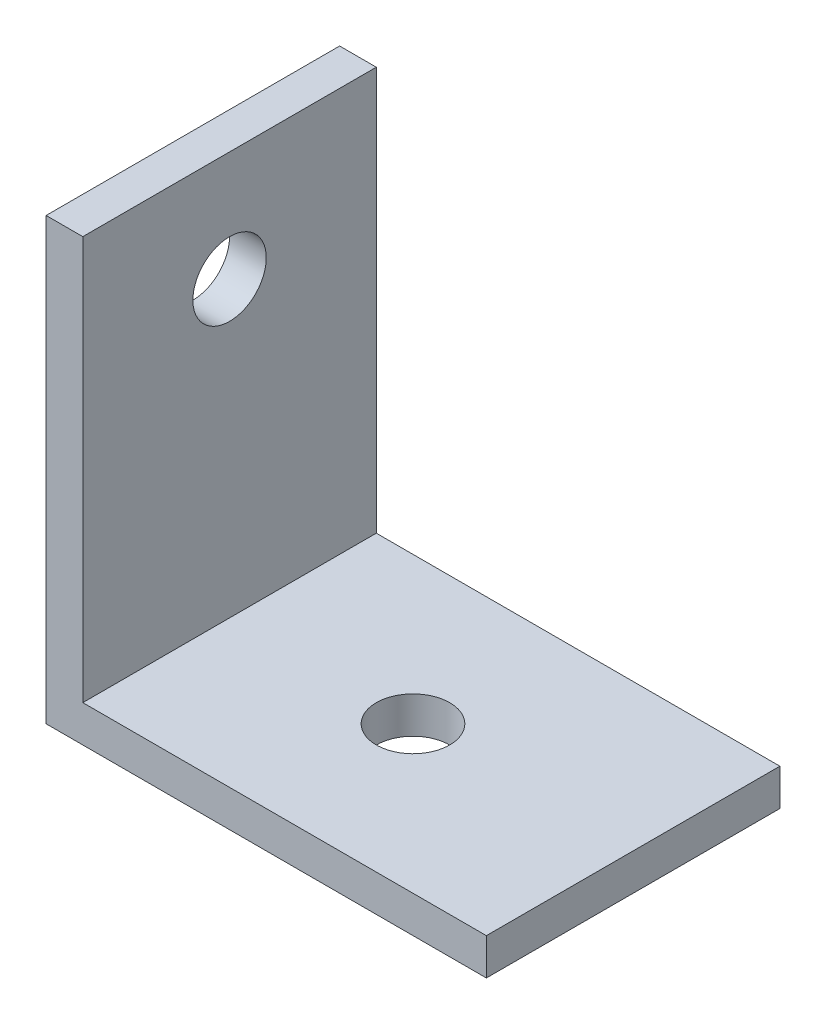
SolidWorks part; units mm, degrees
ref_plane "Front Plane" through (0, 0, 0) normal (0, 0, 1) x (1, 0, 0)
ref_plane "Top Plane" through (0, 0, 0) normal (0, 1, 0) x (1, 0, 0)
ref_plane "Right Plane" through (0, 0, 0) normal (1, 0, 0) x (0, 0, -1)
sketch "Sketch1" plane through (0, 0, 0) normal (0, 0, 1) x (1, 0, 0)
  line L0 (0, 0) -> (0, 38.1)
  line L1 (0, 38.1) -> (3.175, 38.1)
  line L2 (3.175, 38.1) -> (3.175, 3.175)
  line L3 (3.175, 3.175) -> (38.1, 3.175)
  line L4 (38.1, 3.175) -> (38.1, 0)
  line L5 (38.1, 0) -> (0, 0)
  dimension "D1" = 38.1
  dimension "D2" = 38.1
  dimension "D3" = 3.175
  dimension "D4" = 3.175
extrude "Boss-Extrude1" add sketch "Sketch1" along normal blind 25.4
sketch "Sketch2" plane through (0, 3.175, 0) normal (0, 1, 0) x (1, 0, 0)
  line L0 (38.1, 0) -> (3.175, 0) construction
  line L1 (38.1, -25.4) -> (38.1, 0) construction
  circle A0 centre (19.05, -12.7) radius 3.175
  dimension "D1" = 6.35
  dimension "D2" = 12.7
  dimension "D3" = 19.05
extrude "Cut-Extrude1" cut sketch "Sketch2" against normal through all
sketch "Sketch3" plane through (3.175, 0, 0) normal (1, 0, 0) x (0, 0, -1)
  line L1 (-25.4, 3.175) -> (0, 3.175) construction
  line L2 (-25.4, 3.175) -> (-25.4, 38.1) construction
  circle A0 centre (-12.7, 28.575) radius 3.175
  dimension "D1" = 6.35
  dimension "D2" = 25.4
  dimension "D3" = 12.7
extrude "Cut-Extrude2" cut sketch "Sketch3" against normal through all
sketch "Sketch4" plane through (0, 0, 0) normal (-1, 0, 0) x (0, 0, 1)
  point P0 (12.7, 28.575)
